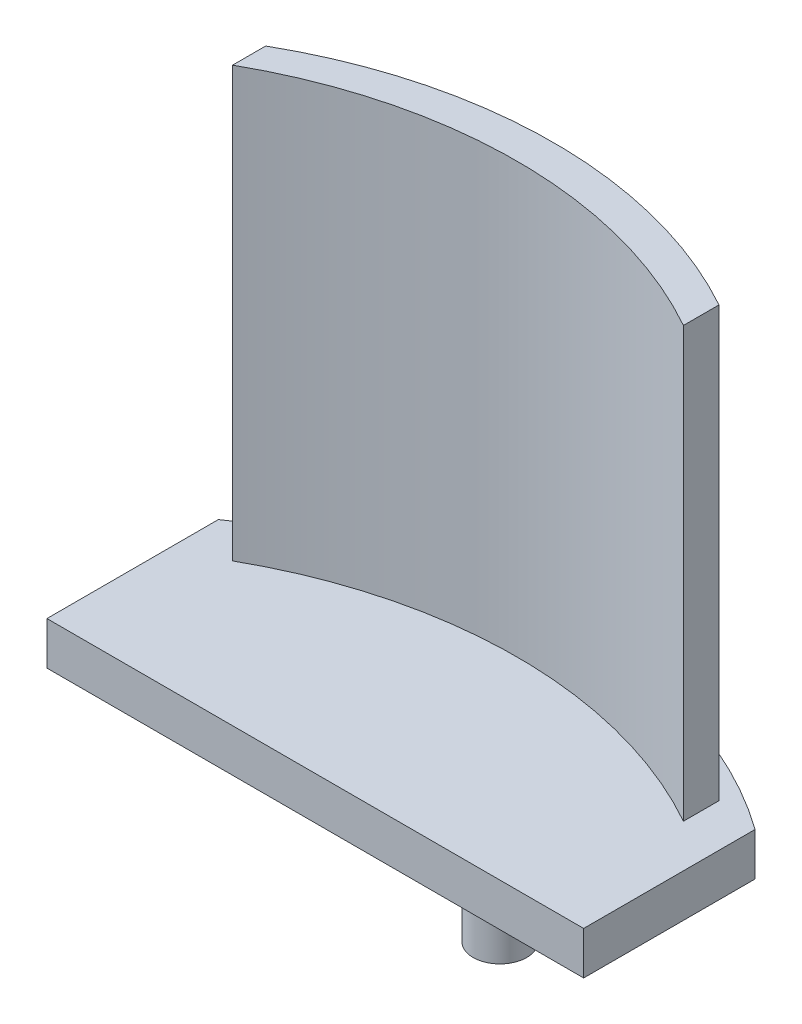
SolidWorks part; units mm, degrees
ref_plane "Front Plane" through (0, 0, 0) normal (0, 0, 1) x (1, 0, 0)
ref_plane "Top Plane" through (0, 0, 0) normal (0, 1, 0) x (1, 0, 0)
ref_plane "Right Plane" through (0, 0, 0) normal (1, 0, 0) x (0, 0, -1)
sketch "Sketch1" plane through (0, 0, 0) normal (0, 1, 0) x (1, 0, 0)
  line L1 (0, 0) -> (31.75, 0)
  line L2 (0, 0) -> (0, 26.6496)
  line L4 (31.75, 0) -> (31.75, 26.6496)
  arc A0 (0, 26.6496) -> (31.75, 26.6496) centre (15.875, 4.4945) cw
  dimension "D3" = 27.2555
  dimension "D4" = 4.4945
  dimension "D5" = 15.875
  dimension "D1" = 31.75
extrude "Boss-Extrude1" add sketch "Sketch1" along normal blind 2.54
sketch "Sketch2" plane through (0, 2.54, 0) normal (0, 1, 0) x (1, 0, 0)
  line L1 (0, 26.6496) -> (0, 0) construction
  line L5 (0, 0) -> (31.75, 0) construction
  line L7 (31.75, 0) -> (31.75, 26.6496) construction
  line L10 (2.54, 26.9117) -> (2.54, 24.9517)
  line L11 (29.21, 27.0547) -> (29.21, 24.9517)
  arc A2 (2.54, 26.9117) -> (29.21, 27.0547) centre (16.002, 3.302) cw
  arc A3 (2.54, 24.9517) -> (29.21, 24.9517) centre (15.875, 1.27) cw
  point P20 (29.21, 26.0032)
  dimension "D2" = 2.54
  dimension "D3" = 2.54
  dimension "D7" = 27.178
  dimension "D8" = 27.178
  dimension "D9" = 3.302
  dimension "D10" = 16.002
  dimension "D11" = 1.27
  dimension "D12" = 15.875
extrude "Boss-Extrude2" add sketch "Sketch2" along normal blind 25.4
sketch "Sketch4" plane through (0, 0, 0) normal (0, -1, 0) x (1, 0, 0)
  line L0 (31.75, 0) -> (31.75, -26.6496) construction
  line L1 (0, 0) -> (31.75, 0)
  line L2 (0, 0) -> (0, -16.51)
  line L3 (0, -16.51) -> (31.75, -16.51)
  line L4 (31.75, 0) -> (31.75, -16.51)
  dimension "D1" = 16.51
extrude "Cut-Extrude1" cut sketch "Sketch4" against normal blind 2.54
sketch "Sketch5" plane through (0, 0, 0) normal (0, -1, 0) x (1, 0, 0)
  line L0 (0, -16.51) -> (31.75, -16.51) construction
  line L1 (31.75, -16.51) -> (31.75, -26.6496) construction
  circle A0 centre (14.732, -28.575) radius 1.5875
  dimension "D2" = 3.175
  dimension "D1" = 12.065
  dimension "D3" = 17.018
extrude "Boss-Extrude3" add sketch "Sketch5" along normal blind 12.7
